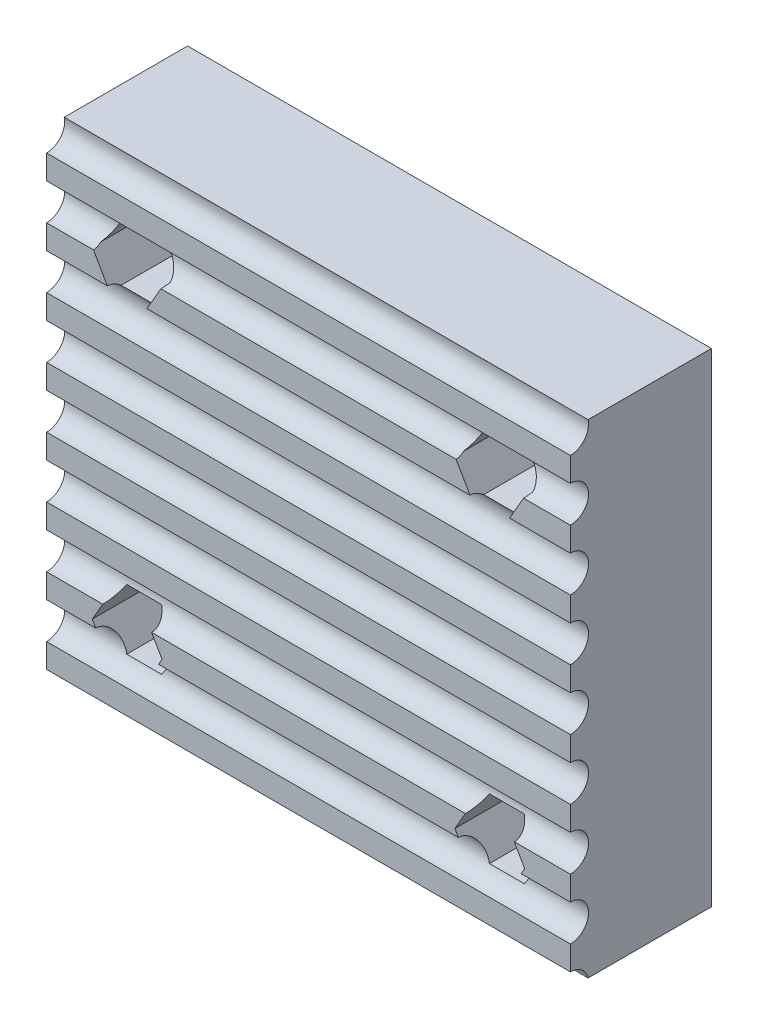
SolidWorks part; units mm, degrees
ref_plane "Front Plane" through (0, 0, 0) normal (0, 0, 1) x (1, 0, 0)
ref_plane "Top Plane" through (0, 0, 0) normal (0, 1, 0) x (1, 0, 0)
ref_plane "Right Plane" through (0, 0, 0) normal (1, 0, 0) x (0, 0, -1)
sketch "Sketch3" plane through (0, 0, 0) normal (0, 0, 1) x (1, 0, 0)
  line L0 (26, 0) -> (26, 24)
  line L1 (0, 0) -> (26, 0)
  line L2 (0, 0) -> (0, 24)
  line L3 (0, 24) -> (26, 24)
  line L4 (13, 0) -> (13, 24)
  line L6 (5.7321, 4) -> (4.866, 5.5)
  line L7 (4.866, 5.5) -> (3.134, 5.5)
  line L8 (3.134, 5.5) -> (2.2679, 4)
  line L9 (2.2679, 4) -> (3.134, 2.5)
  line L10 (3.134, 2.5) -> (4.866, 2.5)
  line L11 (4.866, 2.5) -> (5.7321, 4)
  line L12 (5.7321, 20) -> (4.866, 21.5)
  line L13 (4.866, 21.5) -> (3.134, 21.5)
  line L14 (3.134, 21.5) -> (2.2679, 20)
  line L15 (2.2679, 20) -> (3.134, 18.5)
  line L16 (3.134, 18.5) -> (4.866, 18.5)
  line L17 (4.866, 18.5) -> (5.7321, 20)
  line L18 (23.7321, 20) -> (22.866, 21.5)
  line L19 (22.866, 21.5) -> (21.134, 21.5)
  line L20 (21.134, 21.5) -> (20.2679, 20)
  line L21 (20.2679, 20) -> (21.134, 18.5)
  line L22 (21.134, 18.5) -> (22.866, 18.5)
  line L23 (22.866, 18.5) -> (23.7321, 20)
  line L24 (23.7321, 4) -> (22.866, 5.5)
  line L25 (22.866, 5.5) -> (21.134, 5.5)
  line L26 (21.134, 5.5) -> (20.2679, 4)
  line L27 (20.2679, 4) -> (21.134, 2.5)
  line L28 (21.134, 2.5) -> (22.866, 2.5)
  line L29 (22.866, 2.5) -> (23.7321, 4)
  circle A0 centre (4, 4) radius 1.5 construction
  circle A1 centre (4, 20) radius 1.5 construction
  circle A2 centre (22, 20) radius 1.5 construction
  circle A3 centre (22, 4) radius 1.5 construction
  dimension "D3" = 4
  dimension "D4" = 9
  dimension "D1" = 13
  dimension "D2" = 24
  dimension "D5" = 3
  dimension "D7" = 4
  dimension "D8" = 9
extrude "Boss-Extrude2" add sketch "Sketch3" along normal blind 7
sketch "Sketch5" [suppressed] plane through (26, 0, 0) normal (1, 0, 0) x (0, 0, -1)
  line L0 (-10, 24) -> (-10, 21)
  line L1 (-10, 0) -> (-10, 24) construction
  line L2 (-10, 21) -> (-8, 21)
  line L3 (-8, 21) -> (-8, 19)
  line L4 (-8, 19) -> (-10, 19)
  line L5 (-10, 19) -> (-10, 16)
  line L6 (-10, 16) -> (-8, 16)
  line L7 (-8, 16) -> (-8, 14)
  line L8 (-8, 14) -> (-10, 14)
  line L9 (-10, 14) -> (-10, 11)
  line L10 (-10, 11) -> (-8, 11)
  line L11 (-8, 11) -> (-8, 9)
  line L12 (-8, 9) -> (-10, 9)
  line L13 (-10, 9) -> (-10, 6)
  line L14 (-10, 6) -> (-8, 6)
  line L15 (-8, 6) -> (-8, 4)
  line L16 (-8, 4) -> (-10, 4)
  line L17 (-10, 4) -> (-10, 1)
  line L18 (-10, 1) -> (-8, 1)
  line L19 (-8, 1) -> (-8, -1)
  line L20 (-8, -1) -> (-10, -1)
  line L21 (-10, -1) -> (-10, -4)
  line L22 (-10, -4) -> (-8, -4)
  line L23 (-8, -4) -> (-8, -6)
  line L24 (-8, -6) -> (-10, -6)
  line L25 (-10, 24) -> (-12.9303, 24)
  line L26 (-12.9303, 24) -> (-12.9303, -6)
  line L27 (-12.9303, -6) -> (-10, -6)
  line L28 (-8, -6) -> (-10, -6)
  dimension "D1" = 3
  dimension "D2" = 2
  dimension "D3" = 2
  dimension "D4" = 6
sketch "Sketch7" plane through (26, 0, 0) normal (1, 0, 0) x (0, 0, -1)
  line L0 (-7, 0) -> (-7, 24) construction
  circle A0 centre (-7, 23.8) radius 0.9
  circle A1 centre (-7, 20.8) radius 0.9
  circle A2 centre (-7, 17.8) radius 0.9
  circle A3 centre (-7, 14.8) radius 0.9
  circle A4 centre (-7, 11.8) radius 0.9
  circle A5 centre (-7, 8.8) radius 0.9
  circle A6 centre (-7, 5.8) radius 0.9
  circle A7 centre (-7, 2.8) radius 0.9
  circle A8 centre (-7, -0.2) radius 0.9
  dimension "D1" = 1.8
  dimension "D2" = 0.2
  dimension "D3" = 9
extrude "Cut-Extrude1" cut sketch "Sketch7" against normal through all
